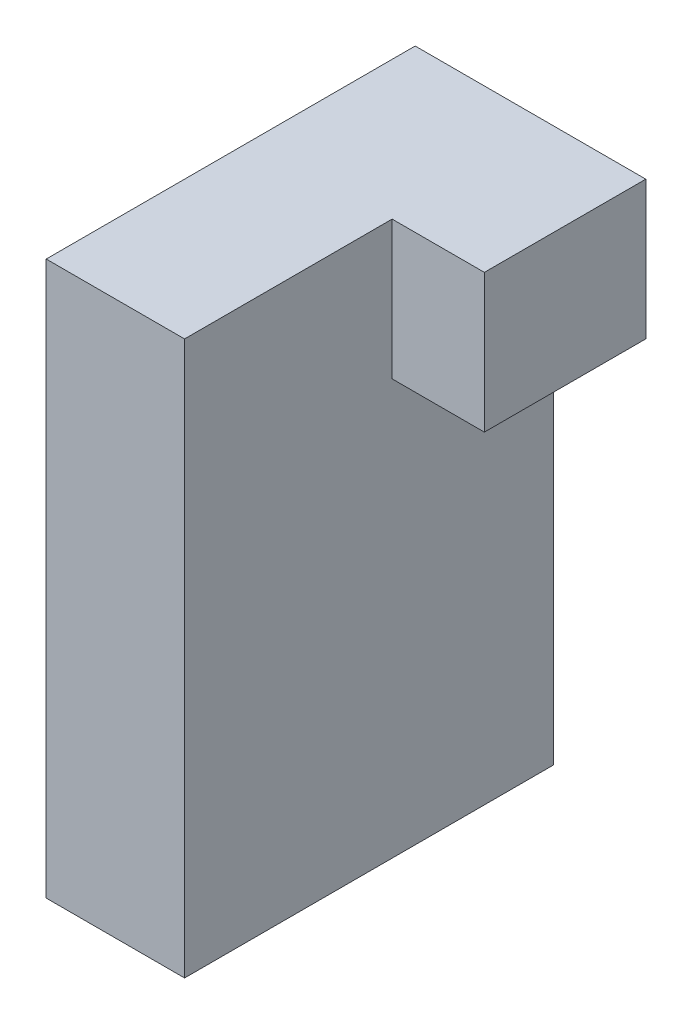
SolidWorks part; units mm, degrees
ref_plane "Front Plane" through (0, 0, 0) normal (0, 0, 1) x (1, 0, 0)
ref_plane "Top Plane" through (0, 0, 0) normal (0, 1, 0) x (1, 0, 0)
ref_plane "Right Plane" through (0, 0, 0) normal (1, 0, 0) x (0, 0, -1)
sketch "Sketch1" plane through (0, 0, 0) normal (1, 0, 0) x (0, 0, -1)
  line L1 (-25.4, 38.1) -> (25.4, 38.1)
  line L2 (-25.4, 38.1) -> (-25.4, -38.1)
  line L3 (-25.4, -38.1) -> (25.4, -38.1)
  line L4 (25.4, 38.1) -> (25.4, -38.1)
  dimension "D1" = 25.4
  dimension "D2" = 25.4
  dimension "D3" = 38.1
  dimension "D4" = 38.1
extrude "Boss-Extrude1" add sketch "Sketch1" along normal mid plane 19.05
sketch "Sketch2" plane through (9.525, 0, 0) normal (1, 0, 0) x (0, 0, -1)
  line L1 (25.4, 38.1) -> (3.175, 38.1)
  line L2 (25.4, 38.1) -> (25.4, 19.05)
  line L3 (25.4, 19.05) -> (3.175, 19.05)
  line L4 (3.175, 38.1) -> (3.175, 19.05)
  dimension "D1" = 3.175
  dimension "D2" = 19.05
extrude "Boss-Extrude2" add sketch "Sketch2" along normal blind 12.7
